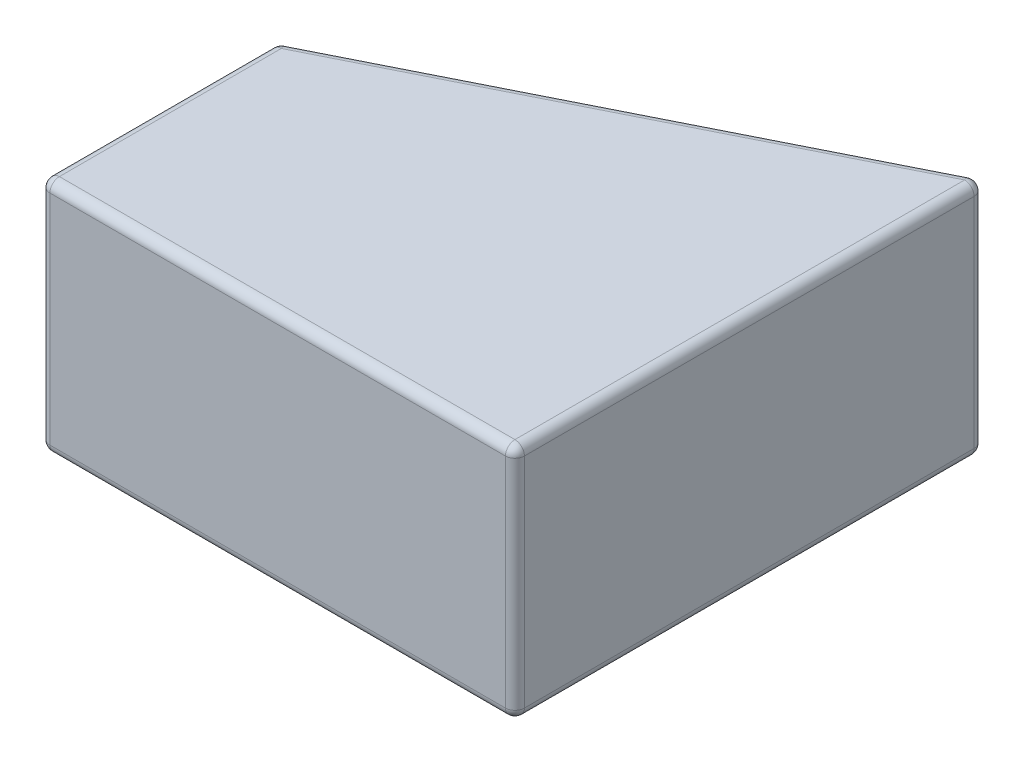
SolidWorks part; units mm, degrees
ref_plane "Front Plane" through (0, 0, 0) normal (0, 0, 1) x (1, 0, 0)
ref_plane "Top Plane" through (0, 0, 0) normal (0, 1, 0) x (1, 0, 0)
ref_plane "Right Plane" through (0, 0, 0) normal (1, 0, 0) x (0, 0, -1)
sketch "Sketch1" plane through (0, 0, 0) normal (0, 1, 0) x (1, 0, 0)
  line L0 (0, 5) -> (10, 10)
  line L1 (0, 0) -> (10, 0)
  line L2 (0, 0) -> (0, 5)
  line L3 (0, 5) -> (10, 5)
  line L4 (10, 0) -> (10, 5)
  line L5 (10, 10) -> (10, 5)
  dimension "D1" = 5
  dimension "D2" = 5
  dimension "D3" = 10
extrude "Boss-Extrude1" add sketch "Sketch1" along normal blind 5 contours L5 L0 L3 | L1 L4 L3 L2
fillet "Fillet1" radius 0.2 12 edges at (5, 0, -7.5) (0, 0, -2.5) (10, 0, -5) (0, 2.5, 0) (5, 5, 0) (10, 2.5, 0) (5, 0, 0) (0, 5, -2.5) (10, 5, -5) (5, 5, -7.5) (0, 2.5, -5) (10, 2.5, -10)
